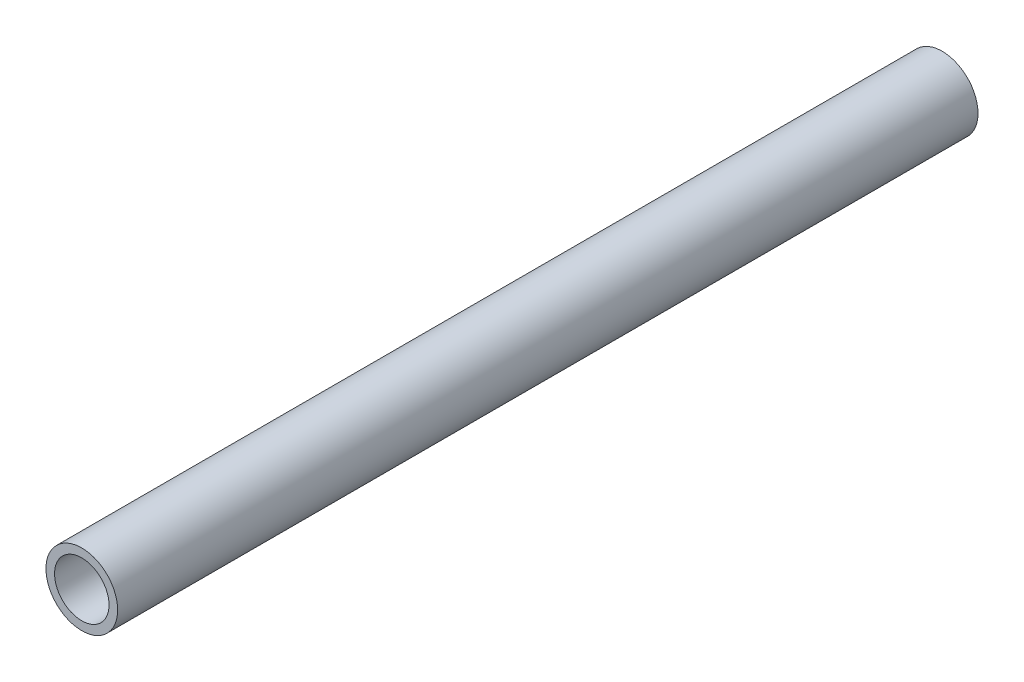
SolidWorks part; units mm, degrees
ref_plane "Plan de face" through (0, 0, 0) normal (0, 0, 1) x (1, 0, 0)
ref_plane "Plan de dessus" through (0, 0, 0) normal (0, 1, 0) x (1, 0, 0)
ref_plane "Plan de droite" through (0, 0, 0) normal (1, 0, 0) x (0, 0, -1)
sketch "Esquisse1" plane through (0, 0, 0) normal (0, 0, 1) x (1, 0, 0)
  circle A0 centre (0, 0) radius 9.5
  circle A1 centre (0, 0) radius 12.5
  dimension "D1" = 25
  dimension "D2" = 19
extrude "Boss.-Extru.2" add sketch "Esquisse1" along normal blind 300
